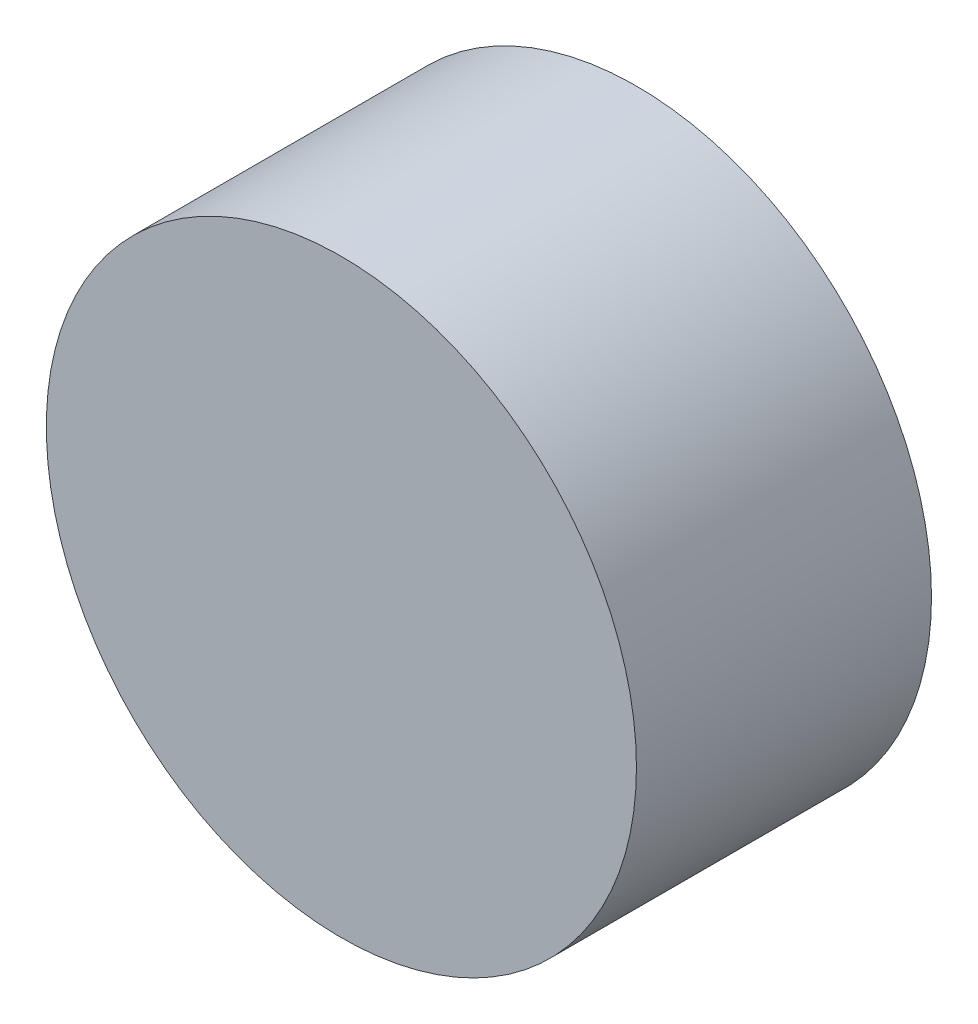
SolidWorks part; units mm, degrees
ref_plane "Front Plane" through (0, 0, 0) normal (0, 0, 1) x (1, 0, 0)
ref_plane "Top Plane" through (0, 0, 0) normal (0, 1, 0) x (1, 0, 0)
ref_plane "Right Plane" through (0, 0, 0) normal (1, 0, 0) x (0, 0, -1)
sketch "Sketch1" plane through (0, 0, 0) normal (0, 0, 1) x (1, 0, 0)
  circle A0 centre (0, 0) radius 20
  dimension "D1" = 40
extrude "Boss-Extrude1" add sketch "Sketch1" along normal blind 20
